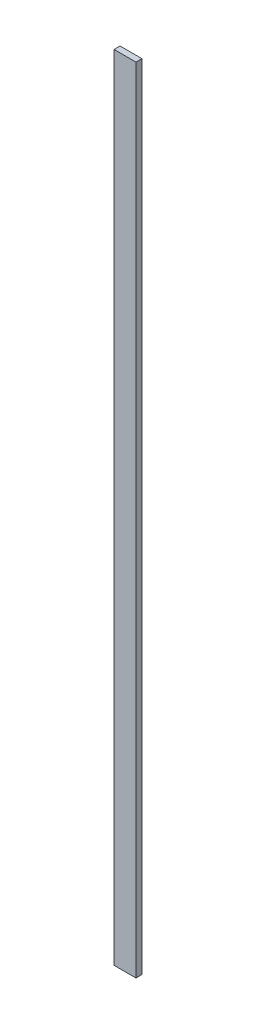
SolidWorks part; units mm, degrees
material "Oak"
ref_plane "Front Plane" through (0, 0, 0) normal (0, 0, 1) x (1, 0, 0)
ref_plane "Top Plane" through (0, 0, 0) normal (0, 1, 0) x (1, 0, 0)
ref_plane "Right Plane" through (0, 0, 0) normal (1, 0, 0) x (0, 0, -1)
sketch "Sketch1" plane through (0, 0, 0) normal (0, 1, 0) x (1, 0, 0)
  line L1 (-69.85, -19.05) -> (69.85, -19.05)
  line L2 (-69.85, -19.05) -> (-69.85, 19.05)
  line L3 (-69.85, 19.05) -> (69.85, 19.05)
  line L4 (69.85, -19.05) -> (69.85, 19.05)
  line L5 (-69.85, -19.05) -> (69.85, 19.05) construction
  line L6 (-69.85, 19.05) -> (69.85, -19.05) construction
  point P0 (0, 0)
  dimension "D1" = 38.1
  dimension "D2" = 139.7
extrude "Boss-Extrude1" add sketch "Sketch1" along normal blind 5054.6 contours L1 L4 L3 L2
